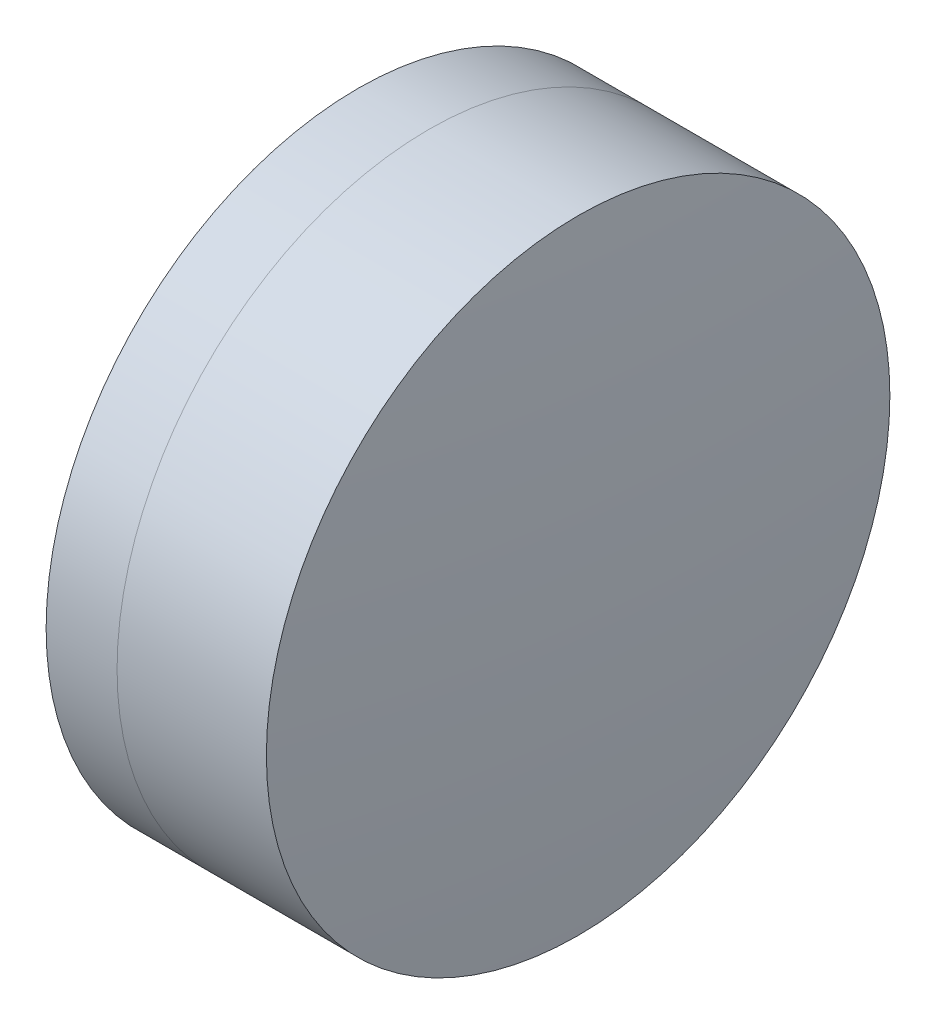
SolidWorks part; units mm, degrees
ref_plane "前视基准面" through (0, 0, 0) normal (0, 0, 1) x (1, 0, 0)
ref_plane "上视基准面" through (0, 0, 0) normal (0, 1, 0) x (1, 0, 0)
ref_plane "右视基准面" through (0, 0, 0) normal (1, 0, 0) x (0, 0, -1)
sketch "草图1" plane through (0, 0, 0) normal (0, 1, 0) x (1, 0, 0)
  line L0 (124.5233, 0) -> (646.9917, 0) construction
  line L1 (266.4093, -4) -> (267.3194, -4)
  line L2 (266.4093, 4) -> (267.3194, 4)
  arc A0 (267.3194, -4) -> (267.3194, 4) centre (257.5031, 0) ccw
  arc A1 (266.4093, 4) -> (266.4093, -4) centre (279.3031, 0) ccw
  point P10 (265.8031, 0)
  point P11 (268.1031, 0)
  dimension "D3" = 13.5
  dimension "D4" = 10.6
  dimension "D1" = 4
  dimension "D2" = 4
  dimension "D5" = 2.3
revolve "旋转1" add sketch "草图1" angle 360 about L0
sketch "草图2" plane through (0, 0, 0) normal (0, 1, 0) x (1, 0, 0)
  line L0 (-0.5519, 0) -> (622.6607, 0) construction
  line L2 (267.3194, 4) -> (269.2354, 4)
  line L3 (267.3194, -4) -> (269.2354, -4)
  arc A0 (269.2354, -4) -> (269.2354, 4) centre (221.6031, 0) ccw
  arc A1 (267.3194, -4) -> (267.3194, 4) centre (257.5031, 0) ccw construction
  arc A2 (267.3194, -4) -> (267.3194, 4) centre (257.5031, 0) ccw
  point P4 (268.1031, 0)
  point P8 (269.4031, 0)
  dimension "D1" = 47.8
  dimension "D2" = 1.3
revolve "旋转3" add sketch "草图2" angle 360 about L0
